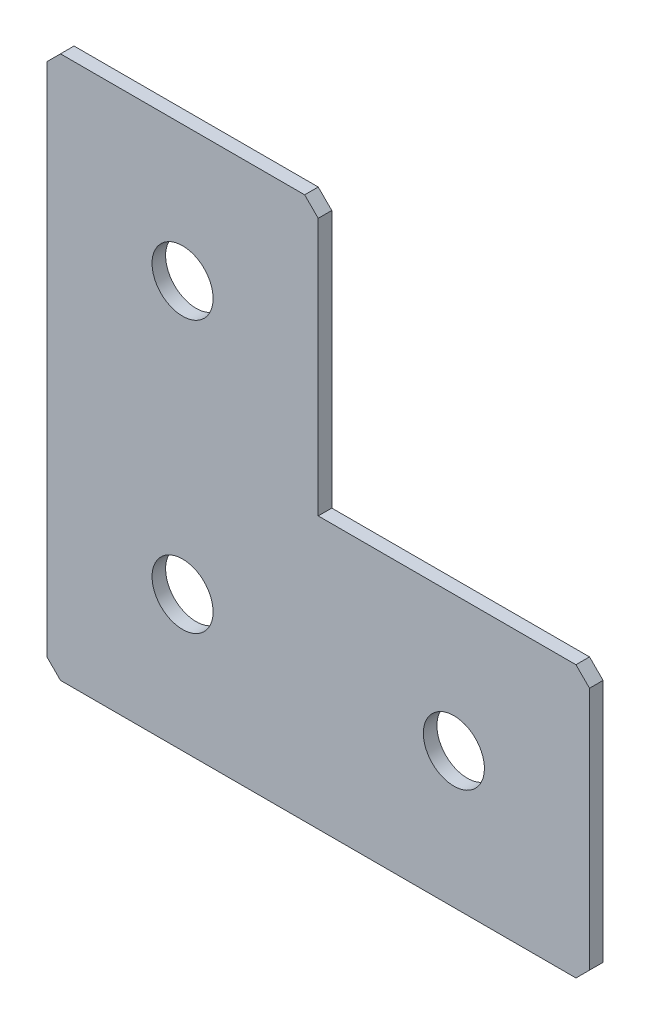
SolidWorks part; units mm, degrees
material "Простая углеродистая сталь"
ref_plane "Спереди(Плоскость XY)" through (0, 0, 0) normal (0, 0, 1) x (1, 0, 0)
ref_plane "Сверху(Плоскость XZ)" through (0, 0, 0) normal (0, 1, 0) x (1, 0, 0)
ref_plane "Справа(Плоскость ZY)" through (0, 0, 0) normal (1, 0, 0) x (0, 0, -1)
sketch "Эскиз1" plane through (0, 0, 0) normal (0, 0, -1) x (1, 0, 0)
  line L0 (0, 0) -> (0, 80)
  line L1 (0, 80) -> (80, 80)
  line L2 (80, 80) -> (80, 40)
  line L3 (80, 40) -> (40, 40)
  line L4 (40, 40) -> (40, 0)
  line L5 (40, 0) -> (0, 0)
  dimension "D1" = 80
  dimension "D2" = 40
  dimension "D3" = 40
  dimension "D4" = 40
extrude "Бобышка-Вытянуть1" add sketch "Эскиз1" along normal blind 2
hole_wizard "Отверстие с зазором M81" positions "Эскиз2" profile "Эскиз3" hole size "M8" standard "DIN" end condition through all
sketch "Эскиз2" plane through (0, 0, -2) normal (0, 0, -1) x (1, 0, 0)
  line L1 (0, 0) -> (40, 0) construction
  line L6 (0, 80) -> (0, 0) construction
  point P4 (20, 60)
  point P6 (20, 20)
  point P29 (60, 60)
  dimension "D1" = 40
  dimension "D2" = 40
  dimension "D4" = 20
  dimension "D5" = 20
sketch "Эскиз3" plane through (20, -60, -2) normal (1, 0, 0) x (0, 1, 0)
  line L0 (0, 0) -> (0, 2)
  line L1 (0, 2) -> (4.5, 2)
  line L2 (4.5, 2) -> (4.5, 0)
  line L5 (4.5, 0) -> (0, 0)
  line L11 (0, -6.35) -> (0, 107.95) construction
  dimension "Диаметр сквозного отверстия" = 9
  dimension "Глубина сквозного отверстия" = 2
chamfer "Фаска1" distance 2 angle 45 5 edges at (0, 0, -1) (40, 0, -1) (80, -40, -1) (80, -80, -1) (0, -80, -1)
